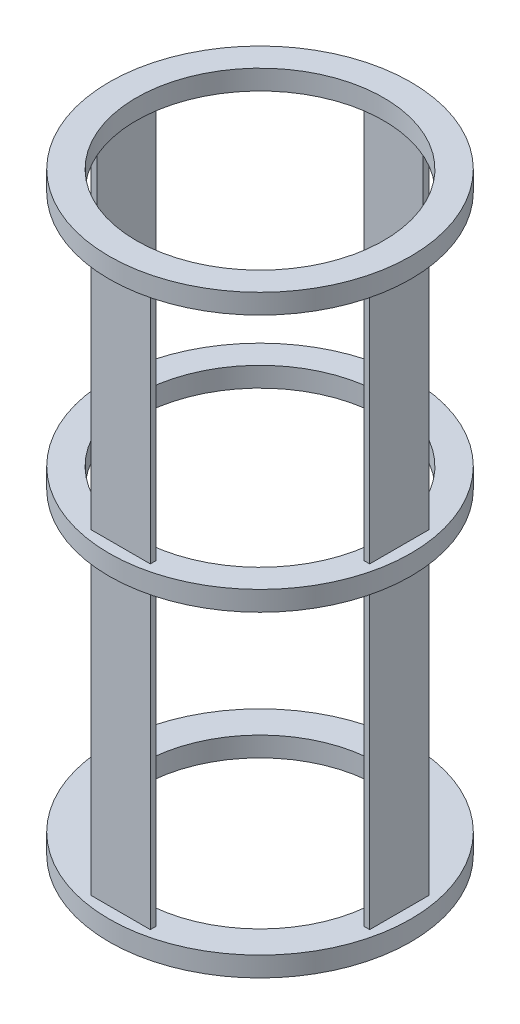
SolidWorks part; units mm, degrees
ref_plane "Plan de face" through (0, 0, 0) normal (0, 0, 1) x (1, 0, 0)
ref_plane "Plan de dessus" through (0, 0, 0) normal (0, 1, 0) x (1, 0, 0)
ref_plane "Plan de droite" through (0, 0, 0) normal (1, 0, 0) x (0, 0, -1)
sketch "Esquisse1" plane through (0, 0, 0) normal (0, 1, 0) x (1, 0, 0)
  circle A0 centre (0, 0) radius 76.2
  circle A1 centre (0, 0) radius 60
  dimension "D1" = 152.4
  dimension "D2" = 120
extrude "Boss.-Extru.1" add sketch "Esquisse1" along normal blind 10
sketch "Esquisse2" plane through (0, 10, 0) normal (0, 1, 0) x (1, 0, 0)
  line L0 (-15, 70.4202) -> (15, 70.4202)
  line L1 (15, 70.4202) -> (15, 67.4202)
  line L2 (15, 67.4202) -> (-15, 67.4202)
  line L3 (-15, 67.4202) -> (-15, 70.4202)
  line L4 (0, 67.4202) -> (0, 0) construction
  circle A0 centre (0, 0) radius 76.2 construction
  dimension "D1" = 30
  dimension "D2" = 72
  dimension "D3" = 3
extrude "Boss.-Extru.2" add sketch "Esquisse2" along normal blind 290
pattern_circular "Répétition circulaire1" count 4 over 360 about axis through (0, 0, 0) along (0, 1, 0) of "Boss.-Extru.2"
ref_plane "Plan1" through (0, 160, 0) normal (0, 1, 0) x (1, 0, 0)
sketch "Esquisse5" plane through (0, 160, 0) normal (0, 1, 0) x (1, 0, 0)
  circle A0 centre (0, 0) radius 62.5
  circle A1 centre (0, 0) radius 76.2
  dimension "D1" = 125
extrude "Boss.-Extru.3" add sketch "Esquisse5" along normal blind 10
pattern_linear "Répétition linéaire2" count 2 spacing 130 along (0, 1, 0) of "Boss.-Extru.3"
equation "\"A\"=10"
